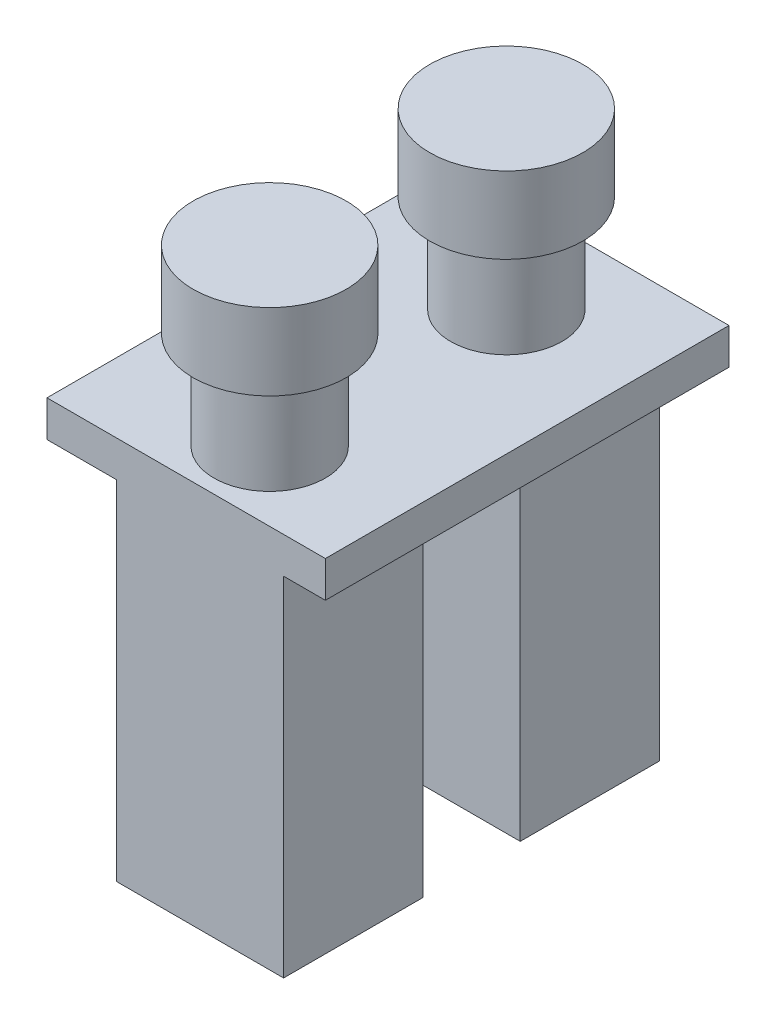
SolidWorks part; units mm, degrees
ref_plane "Přední rovina" through (0, 0, 0) normal (0, 0, 1) x (1, 0, 0)
ref_plane "Vrchní rovina" through (0, 0, 0) normal (0, 1, 0) x (1, 0, 0)
ref_plane "Pravá rovina" through (0, 0, 0) normal (1, 0, 0) x (0, 0, -1)
sketch "Skica1" plane through (0, 0, 0) normal (0, 1, 0) x (1, 0, 0)
  line L1 (0, 0) -> (20, 0)
  line L2 (0, 0) -> (0, 29)
  line L3 (0, 29) -> (20, 29)
  line L4 (20, 0) -> (20, 29)
  dimension "D1" = 20
  dimension "D2" = 29
extrude "Přidat vysunutím1" add sketch "Skica1" along normal blind 2.6
sketch "Skica2" plane through (0, 2.6, 0) normal (0, 1, 0) x (1, 0, 0)
  line L0 (0, 0) -> (20, 0) construction
  line L1 (0, 29) -> (0, 0) construction
  circle A0 centre (11, 5) radius 4
  circle A1 centre (11, 22) radius 4
  point P6 (4.9916, 7.1786)
  point P9 (9.2884, 21.9136)
  point P10 (0, 0)
  point P11 (0, 0)
  dimension "D1" = 8
  dimension "D2" = 8
  dimension "D3" = 17
  dimension "D4" = 5
  dimension "D5" = 11
extrude "Přidat vysunutím2" add sketch "Skica2" along normal blind 7
sketch "Skica3" plane through (0, 9.6, 0) normal (0, 1, 0) x (1, 0, 0)
  circle A0 centre (11, 22) radius 5.5
  circle A1 centre (11, 5) radius 5.5
  dimension "D1" = 11
  dimension "D2" = 11
extrude "Přidat vysunutím3" add sketch "Skica3" along normal blind 5.5
sketch "Skica5" plane through (0, 0, 0) normal (0, -1, 0) x (1, 0, 0)
  line L1 (5, -27) -> (17, -27)
  line L2 (5, -27) -> (5, -17)
  line L3 (5, -17) -> (17, -17)
  line L4 (17, -27) -> (17, -17)
  line L5 (5, -10) -> (17, -10)
  line L6 (5, -10) -> (5, 0)
  line L7 (5, 0) -> (17, 0)
  line L8 (17, -10) -> (17, 0)
  line L9 (0, 0) -> (20, 0) construction
  point P8 (3.9926, 0)
  point P10 (4.283, -29)
  point P11 (4.283, -12.4805)
  point P12 (3.6997, -12.8305)
  point P13 (0, 0)
  point P16 (11, 0)
  point P17 (5, -26.8575)
  point P18 (0, 0)
  point P20 (5, -16.7585)
  dimension "D1" = 10
  dimension "D2" = 12
  dimension "D3" = 7
extrude "Přidat vysunutím4" add sketch "Skica5" along normal blind 25
